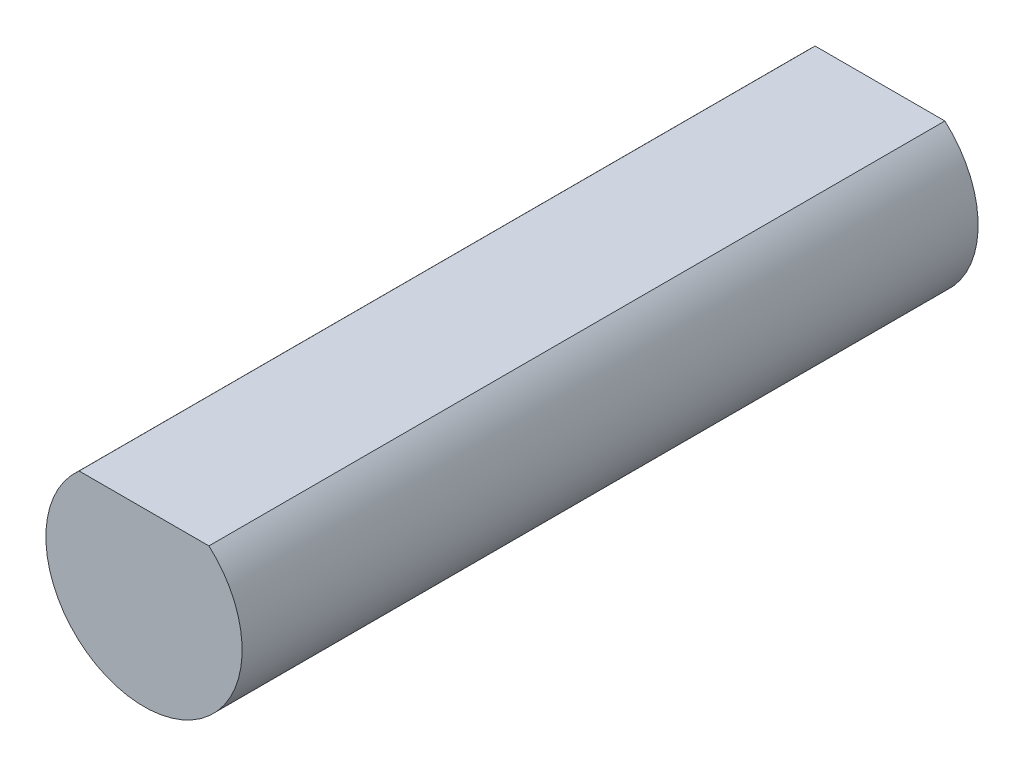
SolidWorks part; units mm, degrees
ref_plane "Front Plane" through (0, 0, 0) normal (0, 0, 1) x (1, 0, 0)
ref_plane "Top Plane" through (0, 0, 0) normal (0, 1, 0) x (1, 0, 0)
ref_plane "Right Plane" through (0, 0, 0) normal (1, 0, 0) x (0, 0, -1)
sketch "Sketch1" plane through (0, 0, 0) normal (0, 0, 1) x (1, 0, 0)
  line L0 (-1.3229, 1.5) -> (1.3229, 1.5)
  line L1 (0, 0) -> (0, 2.402) construction
  arc A0 (1.3229, 1.5) -> (-1.3229, 1.5) centre (0, 0) cw
  point P4 (0, 1.5)
  dimension "D1" = 2
  dimension "D2" = 1.5
extrude "Boss-Extrude1" add sketch "Sketch1" along normal blind 15
equation "\"height\" = 15mm"
equation "\"D1@Boss-Extrude1\"=\"height\""
